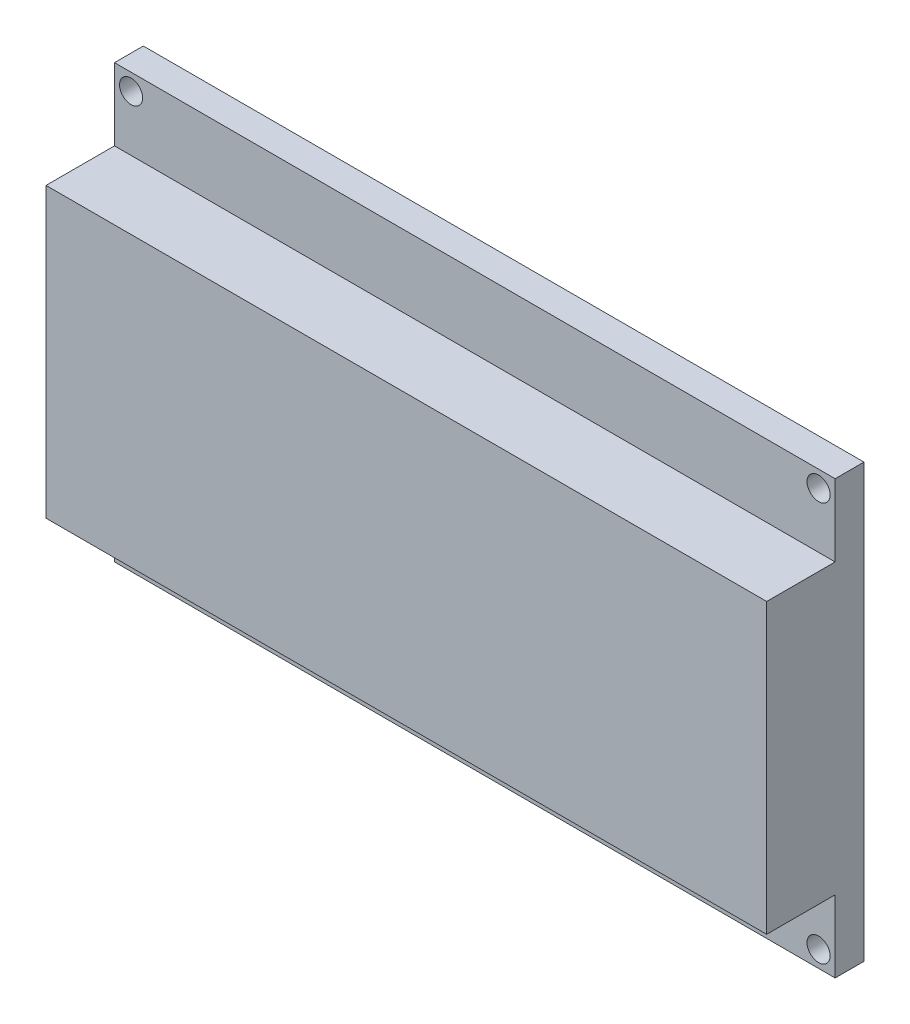
SolidWorks part; units mm, degrees
ref_plane "Plan de face" through (0, 0, 0) normal (0, 0, 1) x (1, 0, 0)
ref_plane "Plan de dessus" through (0, 0, 0) normal (0, 1, 0) x (1, 0, 0)
ref_plane "Plan de droite" through (0, 0, 0) normal (1, 0, 0) x (0, 0, -1)
sketch "Esquisse1" plane through (0, 0, 0) normal (0, 0, 1) x (1, 0, 0)
  line L1 (0, 0) -> (100, 0)
  line L2 (0, 0) -> (0, 60)
  line L3 (0, 60) -> (100, 60)
  line L4 (100, 0) -> (100, 60)
  circle A0 centre (2.3, 57.7) radius 1.6
  circle A1 centre (97.7, 57.7) radius 1.6
  circle A2 centre (97.7, 2.3) radius 1.6
  circle A3 centre (2.3, 2.3) radius 1.6
  dimension "D3" = 3.2
  dimension "D1" = 100
  dimension "D2" = 60
  dimension "D4" = 2.3
  dimension "D5" = 2.3
  dimension "D8" = 2.3
  dimension "D9" = 2.3
  dimension "D10" = 2.3
  dimension "D11" = 2.3
  dimension "D6" = 2
  dimension "D7" = 2
extrude "Boss.-Extru.1" add sketch "Esquisse1" along normal blind 4
sketch "Esquisse2" plane through (0, 0, 4) normal (0, 0, 1) x (1, 0, 0)
  line L0 (0, 0) -> (100, 0) construction
  line L1 (0, 50) -> (100, 50)
  line L2 (0, 50) -> (0, 10)
  line L3 (0, 10) -> (100, 10)
  line L4 (100, 50) -> (100, 10)
  line L6 (0, 60) -> (0, 0) construction
  line L7 (100, 0) -> (100, 60) construction
  point P8 (0, 30)
  dimension "D1" = 10
  dimension "D2" = 40
extrude "Boss.-Extru.2" add sketch "Esquisse2" along normal blind 9.5
